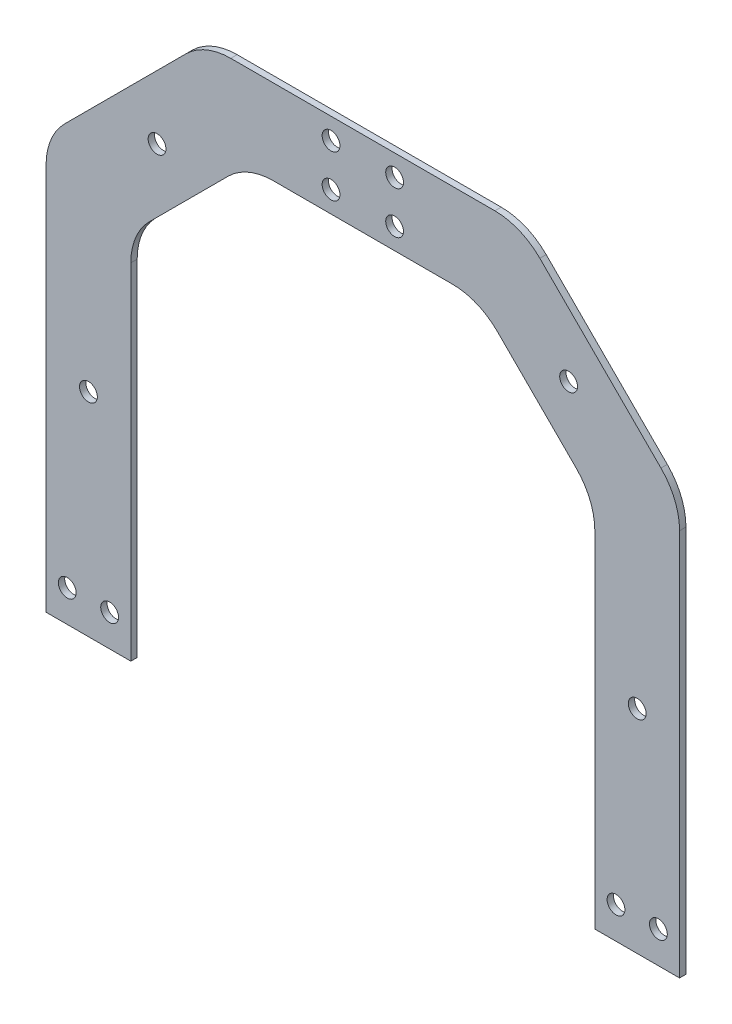
SolidWorks part; units mm, degrees
ref_plane "Alzado" through (0, 0, 0) normal (0, 0, 1) x (1, 0, 0)
ref_plane "Planta" through (0, 0, 0) normal (0, 1, 0) x (1, 0, 0)
ref_plane "Vista lateral" through (0, 0, 0) normal (1, 0, 0) x (0, 0, -1)
sketch "Croquis1" plane through (0, 0, 0) normal (0, 0, 1) x (1, 0, 0)
  line L0 (-119.5, 0) -> (119.5, 0) construction
  line L1 (-119.5, 0) -> (-139.5, 0) construction
  line L2 (0, -1000) -> (0, 49000) construction
  line L3 (119.5, 0) -> (139.5, 0) construction
  line L4 (-149.5, 0) -> (-109.5, 0) construction
  line L5 (149.5, 0) -> (109.5, 0) construction
  line L6 (0, 0) -> (0, 250) construction
  line L7 (0, 230) -> (0, 270) construction
  line L8 (-109.5, 0) -> (-109.5, 230) construction
  line L9 (-109.5, 230) -> (0, 230) construction
  line L10 (-63.5368, 221.2132) -> (-100.7132, 184.0368)
  line L11 (42.3236, 230) -> (-42.3236, 230)
  line L12 (-109.5, 162.8236) -> (-109.5, 0)
  line L13 (-149.5, 0) -> (-149.5, 270) construction
  line L14 (-149.5, 270) -> (0, 270) construction
  line L15 (-83.5368, 261.2132) -> (-140.7132, 204.0368)
  line L16 (62.3236, 270) -> (-62.3236, 270)
  line L17 (-149.5, 182.8236) -> (-149.5, 0)
  line L18 (149.5, 182.8236) -> (149.5, 0)
  line L19 (109.5, 162.8236) -> (109.5, 0)
  line L20 (83.5368, 261.2132) -> (140.7132, 204.0368)
  line L21 (63.5368, 221.2132) -> (100.7132, 184.0368)
  line L22 (-109.5, 0) -> (-149.5, 0)
  line L23 (109.5, 0) -> (149.5, 0)
  arc A0 (149.5, 182.8236) -> (140.7132, 204.0368) centre (119.5, 182.8236) ccw
  arc A1 (109.5, 162.8236) -> (100.7132, 184.0368) centre (79.5, 162.8236) ccw
  arc A2 (63.5368, 221.2132) -> (42.3236, 230) centre (42.3236, 200) ccw
  arc A3 (83.5368, 261.2132) -> (62.3236, 270) centre (62.3236, 240) ccw
  arc A4 (-83.5368, 261.2132) -> (-62.3236, 270) centre (-62.3236, 240) cw
  arc A5 (-140.7132, 204.0368) -> (-149.5, 182.8236) centre (-119.5, 182.8236) ccw
  arc A6 (-100.7132, 184.0368) -> (-109.5, 162.8236) centre (-79.5, 162.8236) ccw
  arc A7 (-63.5368, 221.2132) -> (-42.3236, 230) centre (-42.3236, 200) cw
  point P4 (0, 0)
  point P11 (-129.5, 0)
  point P17 (0, 250)
  point P30 (149.5, 195.25)
  point P33 (109.5, 175.25)
  point P36 (54.75, 230)
  point P39 (74.75, 270)
  point P42 (-74.75, 270)
  point P45 (-149.5, 195.25)
  point P48 (-109.5, 175.25)
  point P51 (-54.75, 230)
  dimension "D8" = 30
  dimension "D1" = 239
  dimension "D2" = 20
  dimension "D3" = 40
  dimension "D4" = 250
  dimension "D5" = 40
  dimension "D6" = 45
  dimension "D7" = 45
extrude "Saliente-Extruir1" add sketch "Croquis1" along normal blind 3
hole_wizard "Taladro de margen para M81" positions "Croquis2" profile "Croquis3" hole size "M8" standard "ISO" end condition through all
sketch "Croquis2" plane through (0, 0, 3) normal (0, 0, 1) x (1, 0, 0)
  line L0 (0, 0) -> (0, 15) construction
  line L2 (-119.5, 15) -> (-139.5, 15) construction
  line L4 (119.5, 15) -> (-119.5, 15) construction
  line L17 (0, 230) -> (0, 270) construction
  line L18 (-42.3236, 230) -> (42.3236, 230) construction
  line L19 (62.3236, 270) -> (-62.3236, 270) construction
  line L21 (-15, 240) -> (15, 240) construction
  line L22 (-15, 240) -> (-15, 260) construction
  line L23 (-15, 260) -> (15, 260) construction
  line L24 (15, 240) -> (15, 260) construction
  line L25 (-15, 240) -> (15, 260) construction
  line L26 (-15, 260) -> (15, 240) construction
  line L33 (-129.5, 185.25) -> (-129.5, 15) construction
  line L35 (0, 250) -> (-64.75, 250) construction
  line L38 (-64.75, 250) -> (-129.5, 185.25) construction
  line L40 (-100.7132, 184.0368) -> (-63.5368, 221.2132) construction
  line L41 (-83.5368, 261.2132) -> (-140.7132, 204.0368) construction
  point P0 (-119.5, 15)
  point P2 (-139.5, 15)
  point P35 (0, 15)
  point P137 (139.5, 15)
  point P144 (-15, 260)
  point P147 (-15, 240)
  point P150 (15, 240)
  point P153 (15, 260)
  point P169 (-129.5, 100.125)
  point P185 (-97.125, 217.625)
  point P190 (129.5, 100.125)
  point P191 (97.125, 217.625)
  point P194 (119.5, 15)
  point P196 (0, 0)
  point P197 (0, 0)
  dimension "D1" = 239
  dimension "D2" = 15
  dimension "D3" = 20
  dimension "D9" = 20
  dimension "D10" = 30
sketch "Croquis3" plane through (-119.5, 15, 3) normal (1, 0, 0) x (0, -1, 0)
  line L0 (0, 0) -> (0, 3)
  line L1 (0, 3) -> (4.2, 3)
  line L2 (4.2, 3) -> (4.2, 0)
  line L5 (4.2, 0) -> (0, 0)
  line L11 (0, -6.35) -> (0, 107.95) construction
  dimension "Diámetro de taladro hasta el siguiente" = 8.4
  dimension "Profundidad de taladro hasta el siguiente" = 3
